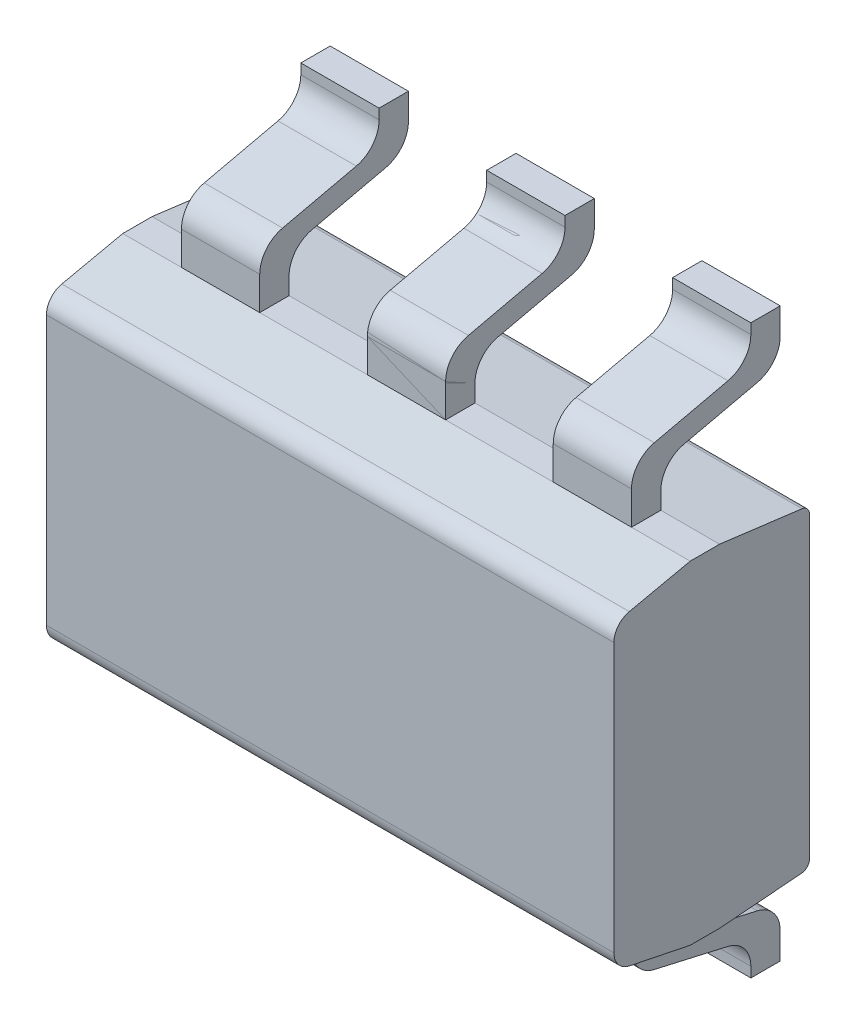
SolidWorks part; units mm, degrees
ref_plane "Plan de face" through (0, 0, 0) normal (0, 0, 1) x (1, 0, 0)
ref_plane "Plan de dessus" through (0, 0, 0) normal (0, 1, 0) x (1, 0, 0)
ref_plane "Plan de droite" through (0, 0, 0) normal (1, 0, 0) x (0, 0, -1)
sketch "Esquisse1" plane through (0, 0, 0) normal (0, 0, 1) x (1, 0, 0)
  line L1 (-1.45, 0.85) -> (1.45, 0.85)
  line L2 (-1.45, 0.85) -> (-1.45, -0.85)
  line L3 (-1.45, -0.85) -> (1.45, -0.85)
  line L4 (1.45, 0.85) -> (1.45, -0.85)
  line L5 (-1.45, 0.85) -> (1.45, -0.85) construction
  line L6 (-1.45, -0.85) -> (1.45, 0.85) construction
  point P0 (0, 0)
  dimension "D1" = 2.9
  dimension "D2" = 1.7
extrude "Boss.-Extru.1" add sketch "Esquisse1" along normal mid plane 0.15
sketch "Esquisse3" plane through (0, 0, 0) normal (1, 0, 0) x (0, 0, -1)
  line L0 (0.075, 0.85) -> (0.075, -0.85)
  line L1 (0.075, -0.85) -> (0.4942, -0.816)
  line L2 (0.535, -0.7717) -> (0.535, 0.7522)
  line L3 (0.4962, 0.7963) -> (0.075, 0.85)
  line L4 (-0.075, 0.85) -> (-0.075, -0.85)
  line L11 (-0.075, 0.85) -> (-0.3862, 0.7824)
  line L12 (-0.465, 0.6847) -> (-0.465, -0.6884)
  line L13 (-0.3851, -0.7864) -> (-0.075, -0.85)
  arc A1 (0.4942, -0.816) -> (0.535, -0.7717) centre (0.4906, -0.7717) ccw
  arc A2 (0.535, 0.7522) -> (0.4962, 0.7963) centre (0.4906, 0.7522) ccw
  arc A3 (-0.3862, 0.7824) -> (-0.465, 0.6847) centre (-0.365, 0.6847) ccw
  arc A4 (-0.465, -0.6884) -> (-0.3851, -0.7864) centre (-0.365, -0.6884) ccw
  dimension "D3" = 0.1
  dimension "D1" = 1
  dimension "D2" = 0.46
extrude "Boss.-Extru.2" add sketch "Esquisse3" along normal mid plane 2.9
ref_plane "Plan1" through (0, 0, 0) normal (1, 0, 0) x (0, 0, -1)
sketch "Esquisse5" plane through (0, 0, 0) normal (1, 0, 0) x (0, 0, -1)
  line L4 (-0.075, 0.85) -> (-0.075, 1.0196)
  line L10 (0.0416, 1.1659) -> (0.4184, 1.2518)
  line L15 (0.535, 1.3981) -> (0.535, 1.45)
  line L16 (0.535, 1.45) -> (0.685, 1.45)
  line L17 (0.685, 1.45) -> (0.685, 1.3155)
  line L18 (0.5684, 1.1693) -> (0.1916, 1.0833)
  line L19 (0.075, 0.9371) -> (0.075, 0.85)
  line L20 (-0.075, 0.85) -> (0.075, 0.85)
  line L21 (0.535, -0.7717) -> (0.535, 0.7522) construction
  arc A4 (0.685, 1.3155) -> (0.5684, 1.1693) centre (0.535, 1.3155) cw
  arc A5 (0.4184, 1.2518) -> (0.535, 1.3981) centre (0.385, 1.3981) ccw
  arc A6 (0.1916, 1.0833) -> (0.075, 0.9371) centre (0.225, 0.9371) ccw
  arc A7 (-0.075, 1.0196) -> (0.0416, 1.1659) centre (0.075, 1.0196) cw
  dimension "D4" = 0.15
  dimension "D1" = 0.15
  dimension "D2" = 0.6
  dimension "D3" = 0.15
extrude "Boss.-Extru.3" add sketch "Esquisse5" along normal mid plane 0.4 separate body
pattern_linear "Répétition linéaire1" count 2 spacing 0.95 along (-1, 0, 0) count 2 spacing 0.95 along (1, 0, 0) of "Boss.-Extru.3"
mirror "Symétrie1" about plane through (0, 0, 0) normal (0, 1, 0) of "Répétition linéaire1", "Boss.-Extru.3"
